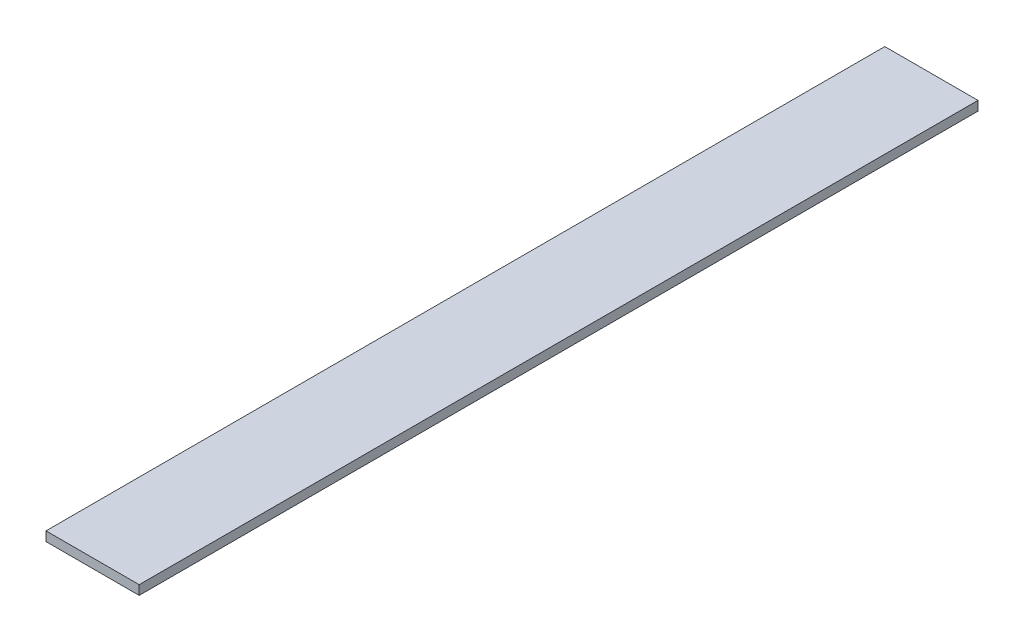
SolidWorks part; units mm, degrees
ref_plane "Front Plane" through (0, 0, 0) normal (0, 0, 1) x (1, 0, 0)
ref_plane "Top Plane" through (0, 0, 0) normal (0, 1, 0) x (1, 0, 0)
ref_plane "Right Plane" through (0, 0, 0) normal (1, 0, 0) x (0, 0, -1)
sketch "Sketch1" plane through (0, 0, 0) normal (0, 1, 0) x (1, 0, 0)
  line L0 (0, 0) -> (0, 457.2)
  line L1 (0, 457.2) -> (-50.8, 457.2)
  line L2 (-50.8, 457.2) -> (-50.8, 0)
  line L3 (-50.8, 0) -> (0, 0)
  dimension "D1" = 50.8
  dimension "D2" = 457.2
extrude "Boss-Extrude1" add sketch "Sketch1" along normal blind 5.08
